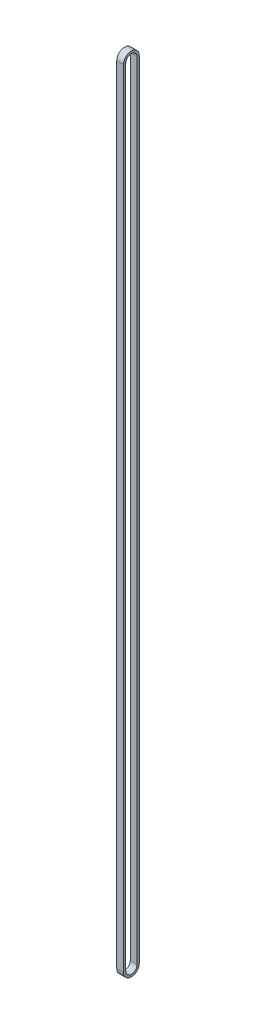
SolidWorks part; units mm, degrees
ref_plane "Front Plane" through (0, 0, 0) normal (0, 0, 1) x (1, 0, 0)
ref_plane "Top Plane" through (0, 0, 0) normal (0, 1, 0) x (1, 0, 0)
ref_plane "Right Plane" through (0, 0, 0) normal (1, 0, 0) x (0, 0, -1)
sketch "Sketch1" plane through (0, 0, 0) normal (1, 0, 0) x (0, 0, -1)
  line L0 (0, 0) -> (0, 698) construction
  line L1 (-5, 0) -> (-5, 698)
  line L2 (5, 0) -> (5, 698)
  line L3 (-7, 0) -> (-7, 698)
  line L4 (7, 0) -> (7, 698)
  arc A0 (-5, 0) -> (5, 0) centre (0, 0) ccw
  arc A1 (5, 698) -> (-5, 698) centre (0, 698) ccw
  arc A2 (7, 698) -> (-7, 698) centre (0, 698) ccw
  arc A3 (-7, 0) -> (7, 0) centre (0, 0) ccw
  point P3 (0, 349)
  dimension "D3" = 712
  dimension "D1" = 2
  dimension "D2" = 14
extrude "Boss-Extrude1" add sketch "Sketch1" along normal mid plane 6
